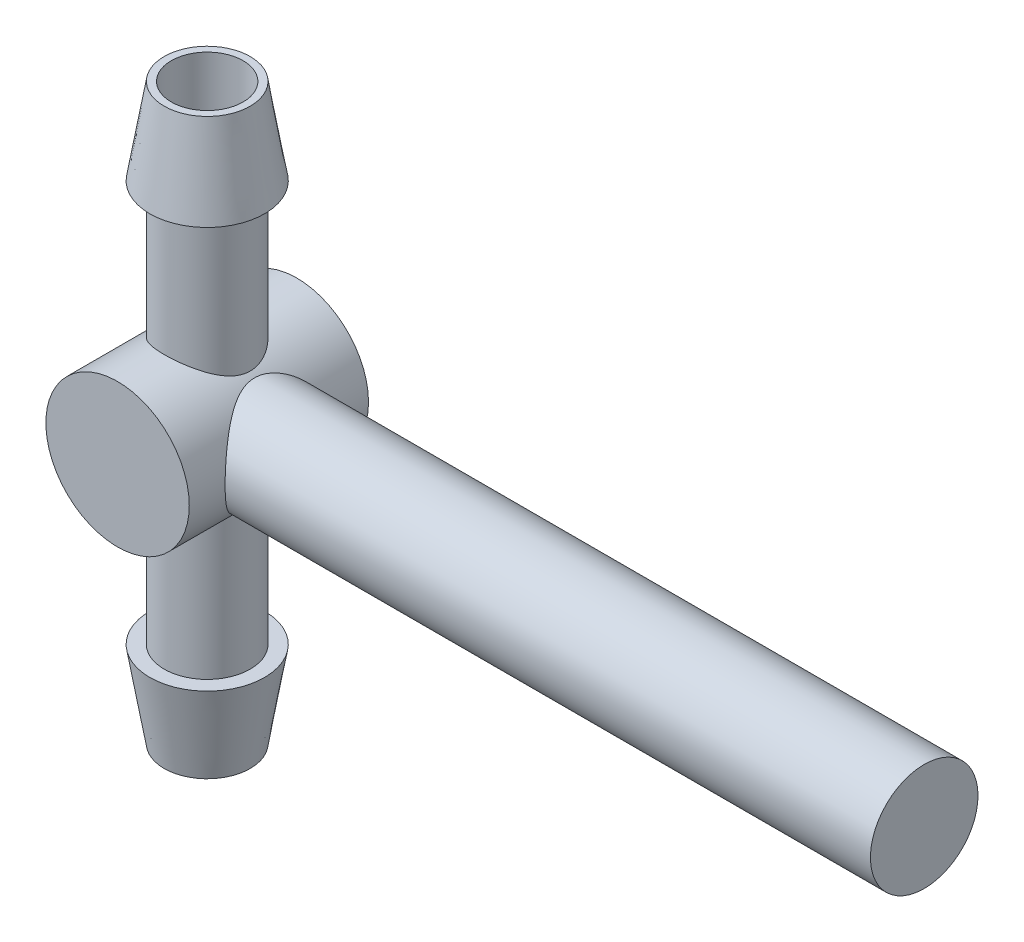
SolidWorks part; units mm, degrees
ref_plane "Front Plane" through (0, 0, 0) normal (0, 0, 1) x (1, 0, 0)
ref_plane "Top Plane" through (0, 0, 0) normal (0, 1, 0) x (1, 0, 0)
ref_plane "Right Plane" through (0, 0, 0) normal (1, 0, 0) x (0, 0, -1)
sketch "Sketch1" plane through (0, 0, 0) normal (0, 0, 1) x (1, 0, 0)
  circle A0 centre (0, 0) radius 5
  dimension "D1" = 10
extrude "Boss-Extrude1" add sketch "Sketch1" along normal mid plane 12.5
sketch "Sketch2" plane through (0, 0, 0) normal (0, 1, 0) x (1, 0, 0)
  circle A0 centre (0, 0) radius 3
  dimension "D1" = 6
extrude "Boss-Extrude2" add sketch "Sketch2" along normal mid plane 40
sketch "Sketch3" plane through (0, 0, 0) normal (1, 0, 0) x (0, 0, -1)
  circle A0 centre (0, 0) radius 3.75
  dimension "D1" = 7.5
extrude "Boss-Extrude3" add sketch "Sketch3" along normal blind 50
sketch "Sketch4" plane through (0, -20, 0) normal (0, -1, 0) x (1, 0, 0)
  circle A0 centre (0, 0) radius 2.5
  dimension "D1" = 5
extrude "Cut-Extrude1" cut sketch "Sketch4" against normal up to next (40 mm away) from surface at 0 starting at face at (0, -20, 3)
sketch "Sketch5" plane through (0, 0, 6.25) normal (0, 0, 1) x (1, 0, 0)
  circle A0 centre (0, 0) radius 3.75
  dimension "D1" = 7.5
extrude "Cut-Extrude2" cut sketch "Sketch5" against normal up to next
sketch "Sketch6" plane through (0, 0, 0) normal (0, 0, 1) x (1, 0, 0)
  line L0 (3, 20) -> (4, 14)
  line L1 (4, 14) -> (3, 14)
  line L2 (3, 4) -> (3, 20) construction
  line L3 (3, 14) -> (3, 20)
  line L4 (0, 20) -> (0, 0)
  line L6 (3, -14) -> (3, -20)
  line L7 (3, -20) -> (4, -14)
  line L8 (4, -14) -> (3, -14)
  line L9 (2.5, 20) -> (-2.5, 20) construction
  line L10 (3, 14) -> (3, 20)
  line L11 (4, 14) -> (3, 14)
  line L12 (3, -14) -> (4, -14)
  line L13 (3, -20) -> (4, -14)
  line L14 (3, -20) -> (3, -14)
  line L15 (0, 20) -> (0, -20)
  line L16 (-3, -20) -> (3, -20) construction
  line L17 (3, -20) -> (3, -4) construction
  line L19 (3, 20) -> (-3, 20) construction
  dimension "D1" = 6
  dimension "D2" = 1
  dimension "D3" = 6
  dimension "D4" = 1
revolve "Revolve1" add sketch "Sketch6" angle 360 about L15
sketch "Sketch7" plane through (0, 0, 6.25) normal (0, 0, 1) x (1, 0, 0)
  circle A0 centre (0, 0) radius 5
extrude "Boss-Extrude4" add sketch "Sketch7" against normal blind 2.5
